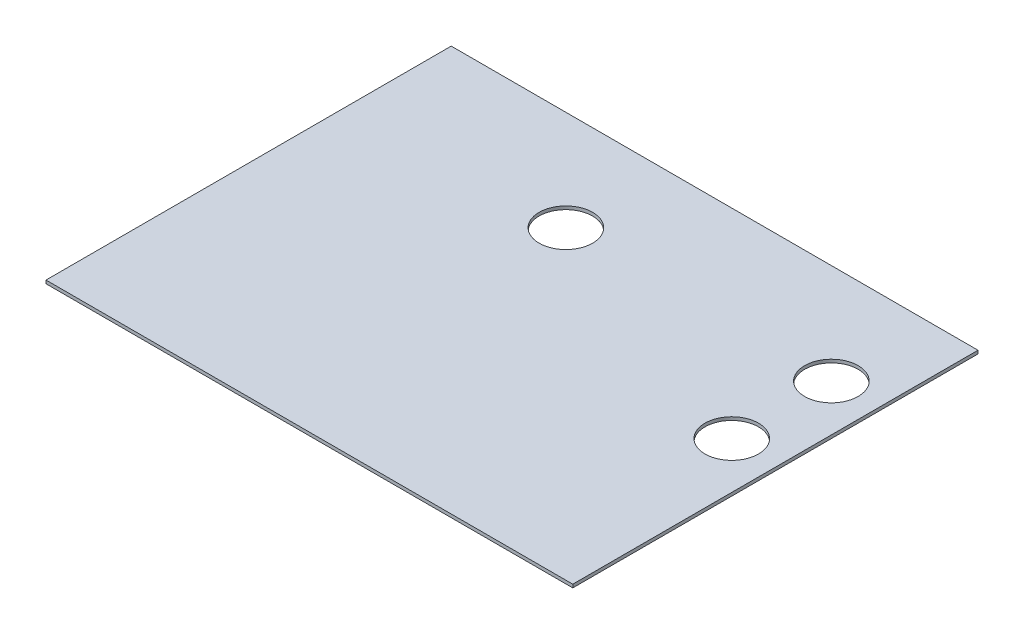
SolidWorks part; units mm, degrees
ref_plane "Front Plane" through (0, 0, 0) normal (0, 0, 1) x (1, 0, 0)
ref_plane "Top Plane" through (0, 0, 0) normal (0, 1, 0) x (1, 0, 0)
ref_plane "Right Plane" through (0, 0, 0) normal (1, 0, 0) x (0, 0, -1)
sketch "Sketch1" plane through (0, 0, 0) normal (0, 1, 0) x (1, 0, 0)
  line L1 (-162.5, 125) -> (162.5, 125)
  line L2 (-162.5, 125) -> (-162.5, -125)
  line L3 (-162.5, -125) -> (162.5, -125)
  line L4 (162.5, 125) -> (162.5, -125)
  line L5 (-162.5, 125) -> (162.5, -125) construction
  line L6 (-162.5, -125) -> (162.5, 125) construction
  point P0 (0, 0)
  dimension "D1" = 250
  dimension "D2" = 325
extrude "Boss-Extrude1" add sketch "Sketch1" along normal blind 2
sketch "Sketch2" plane through (0, 2, 0) normal (0, 1, 0) x (1, 0, 0)
  line L0 (133.7364, 1.8436) -> (133.7364, 69.3545) construction
  line L1 (133.7364, 63.3119) -> (-92.8225, 63.3119) construction
  line L2 (-30.0735, 69.0356) -> (-30.0735, 32.7247) construction
  circle A0 centre (133.7364, 1.8436) radius 16.5
  circle A1 centre (133.7364, 63.3119) radius 16.5
  circle A2 centre (-30.0735, 63.3119) radius 16.5
  dimension "D1" = 33
  dimension "D2" = 33
  dimension "D3" = 33
extrude "Cut-Extrude1" cut sketch "Sketch2" against normal up to next
sketch "Sketch3" plane through (0, 2, 0) normal (0, 1, 0) x (1, 0, 0)
  line L1 (162.5, 125) -> (-57.5, 125)
  line L2 (162.5, 125) -> (162.5, -25)
  line L3 (162.5, -25) -> (-57.5, -25)
  line L4 (-57.5, 125) -> (-57.5, -25)
  circle A0 centre (-30.0735, 63.3119) radius 16.5
  circle A1 centre (133.7364, 63.3119) radius 16.5
  circle A2 centre (133.7364, 1.8436) radius 16.5
  dimension "D1" = 220
  dimension "D2" = 150
